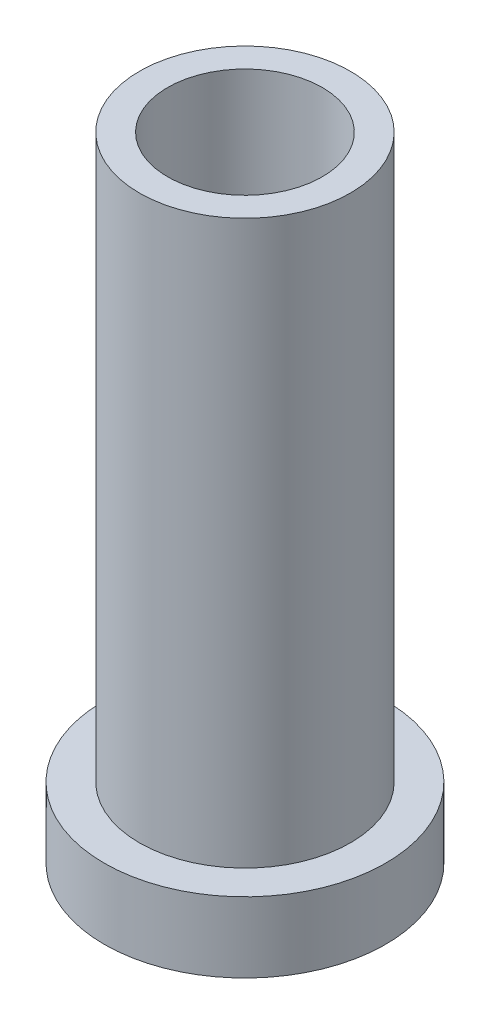
SolidWorks part; units mm, degrees
ref_plane "Front Plane" through (0, 0, 0) normal (0, 0, 1) x (1, 0, 0)
ref_plane "Top Plane" through (0, 0, 0) normal (0, 1, 0) x (1, 0, 0)
ref_plane "Right Plane" through (0, 0, 0) normal (1, 0, 0) x (0, 0, -1)
sketch "Sketch1" plane through (0, 0, 0) normal (0, 1, 0) x (1, 0, 0)
  circle A0 centre (0, 0) radius 10
  dimension "D1" = 20
extrude "Boss-Extrude1" add sketch "Sketch1" along normal mid plane 5
sketch "Sketch2" plane through (0, 2.5, 0) normal (0, 1, 0) x (1, 0, 0)
  circle A0 centre (0, 0) radius 7.5
extrude "Boss-Extrude2" add sketch "Sketch2" along normal blind 40
sketch "Sketch3" plane through (0, -2.5, 0) normal (0, -1, 0) x (-1, 0, 0)
  circle A0 centre (0, 0) radius 5.5
extrude "Cut-Extrude1" cut sketch "Sketch3" against normal through all
